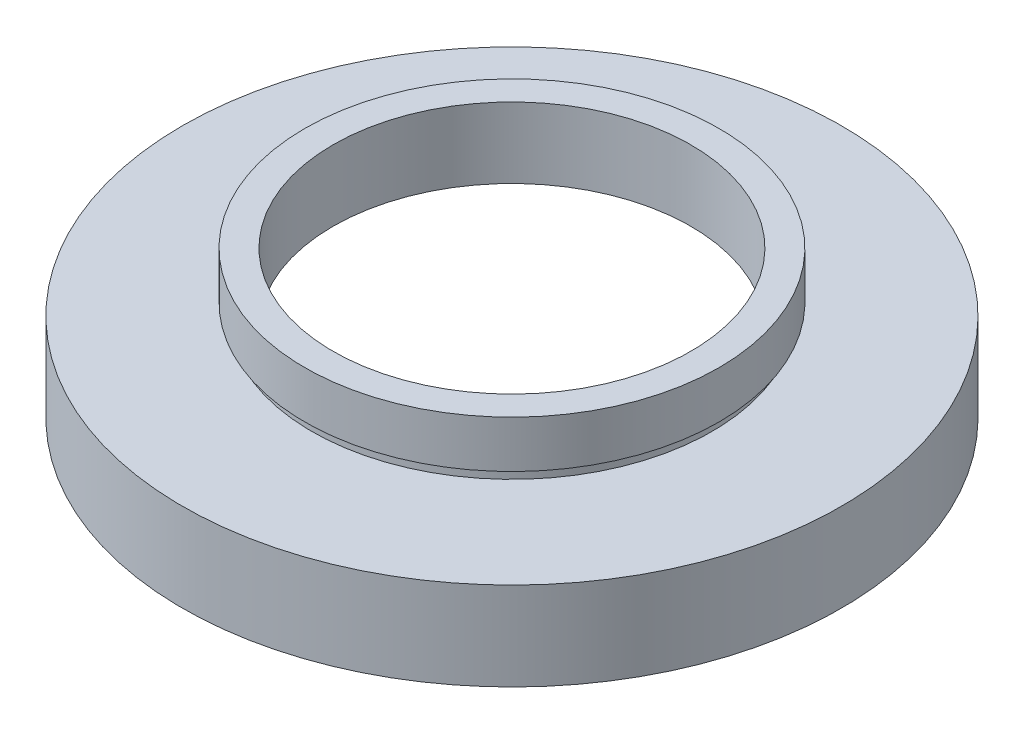
SolidWorks part; units mm, degrees
ref_plane "前视基准面" through (0, 0, 0) normal (0, 0, 1) x (1, 0, 0)
ref_plane "上视基准面" through (0, 0, 0) normal (0, 1, 0) x (1, 0, 0)
ref_plane "右视基准面" through (0, 0, 0) normal (1, 0, 0) x (0, 0, -1)
sketch "草图1" plane through (0, 0, 0) normal (0, 0, 1) x (1, 0, 0)
  line L0 (0, 16.886) -> (0, -24.4878) construction
  line L1 (25.3, 0) -> (25.3, 5.5)
  line L2 (15.2, 6.5) -> (25.95, 6.5)
  line L3 (15.2, 6.5) -> (15.2, 12.5)
  line L4 (15.2, 12.5) -> (17.6, 12.5)
  line L5 (17.6, 12.5) -> (17.6, 8.5)
  line L6 (17.6, 8.5) -> (17, 8.5)
  line L7 (17, 8.5) -> (17, 7.5)
  line L8 (17, 7.5) -> (28, 7.5)
  line L9 (28, 7.5) -> (28, 0)
  line L10 (28, 0) -> (25.3, 0)
  line L11 (25.3, 5.5) -> (25.95, 5.5)
  line L12 (25.95, 5.5) -> (25.95, 6.5)
  line L13 (0, 0) -> (3.4668, 0) construction
  point P4 (26.65, 0)
  dimension "D1" = 15.2
  dimension "D2" = 17.6
  dimension "D3" = 17
  dimension "D4" = 25.3
  dimension "D5" = 25.95
  dimension "D6" = 28
  dimension "D7" = 12.5
  dimension "D8" = 7.5
  dimension "D9" = 1
  dimension "D10" = 5.5
  dimension "D11" = 1
revolve "旋转1" add sketch "草图1" angle 360 about L0
cosmetic thread "装饰螺纹线1" parameters "D2"=35
cosmetic thread "装饰螺纹线2" parameters "D2"=30.5
cosmetic thread "装饰螺纹线3" parameters "D2"=51.69
